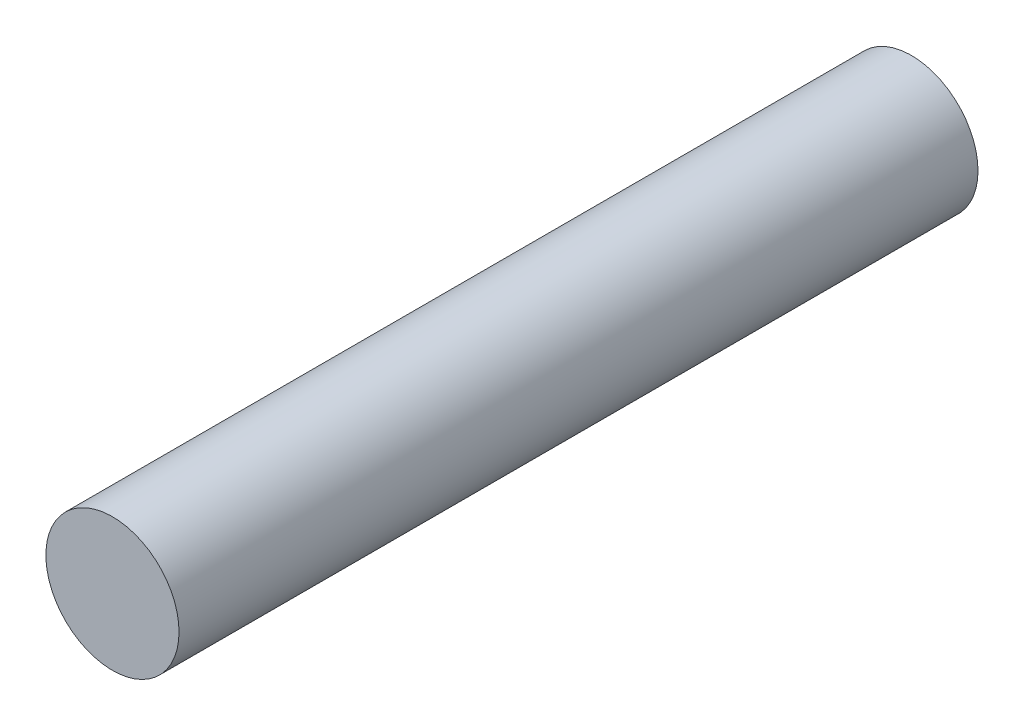
SolidWorks part; units mm, degrees
ref_plane "Front Plane" through (0, 0, 0) normal (0, 0, 1) x (1, 0, 0)
ref_plane "Top Plane" through (0, 0, 0) normal (0, 1, 0) x (1, 0, 0)
ref_plane "Right Plane" through (0, 0, 0) normal (1, 0, 0) x (0, 0, -1)
sketch "Sketch1" plane through (0, 0, 0) normal (0, 0, 1) x (1, 0, 0)
  circle A0 centre (0, 0) radius 1.875
  dimension "D1" = 3.75
extrude "Boss-Extrude1" add sketch "Sketch1" along normal blind 22.5
